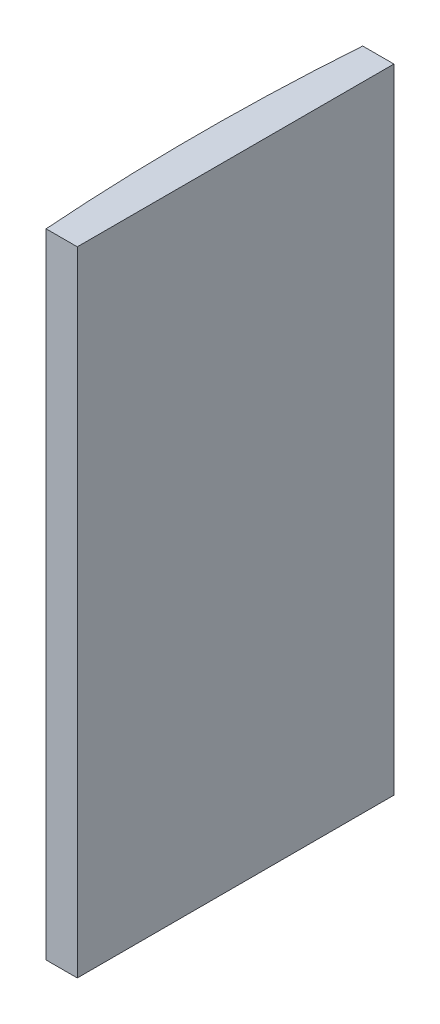
SolidWorks part; units mm, degrees
ref_plane "前视基准面" through (0, 0, 0) normal (0, 0, 1) x (1, 0, 0)
ref_plane "上视基准面" through (0, 0, 0) normal (0, 1, 0) x (1, 0, 0)
ref_plane "右视基准面" through (0, 0, 0) normal (1, 0, 0) x (0, 0, -1)
sketch "草图1" plane through (0, 0, 0) normal (0, 1, 0) x (1, 0, 0)
  line L0 (10.7432, 0) -> (-607.0701, 0) construction
  line L1 (-201.9001, 15) -> (-198.9448, 15)
  line L2 (-201.9001, -15) -> (-198.9448, -15)
  line L3 (-198.9448, 15) -> (-198.9448, -15)
  arc A0 (-201.9001, 15) -> (-201.9001, -15) centre (4.3552, 0) ccw
  point P19 (-202.4448, 0)
  point P20 (-198.9448, 0)
  dimension "D2" = 15
  dimension "D3" = 206.8
  dimension "D4" = 3.5
  dimension "D1" = 15
extrude "凸台-拉伸1" add sketch "草图1" along normal blind 60
